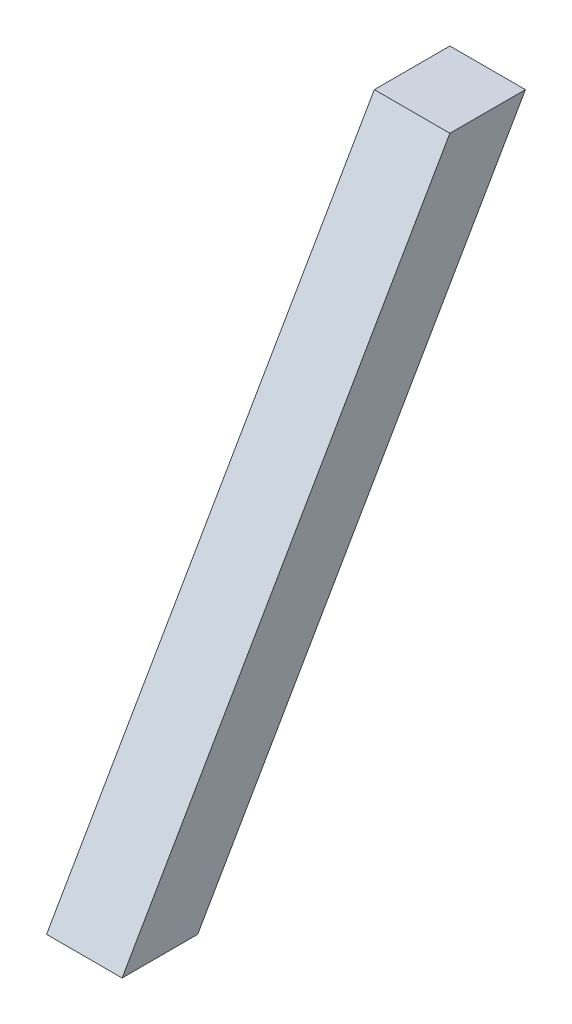
SolidWorks part; units mm, degrees
ref_plane "Front Plane" through (0, 0, 0) normal (0, 0, 1) x (1, 0, 0)
ref_plane "Top Plane" through (0, 0, 0) normal (0, 1, 0) x (1, 0, 0)
ref_plane "Right Plane" through (0, 0, 0) normal (1, 0, 0) x (0, 0, -1)
sketch "Sketch2" plane through (0, 0, 0) normal (1, 0, 0) x (0, 0, -1)
  line L0 (-20, 0) -> (20, 0)
  line L1 (20, 0) -> (193.5, 300.5108)
  line L2 (193.5, 300.5108) -> (153.5, 300.5108)
  line L3 (153.5, 300.5108) -> (-20, 0)
  point P4 (0, 0)
  dimension "D1" = 40
  dimension "D2" = 347
  dimension "D3" = 60
extrude "Boss-Extrude2" add sketch "Sketch2" along normal blind 40
